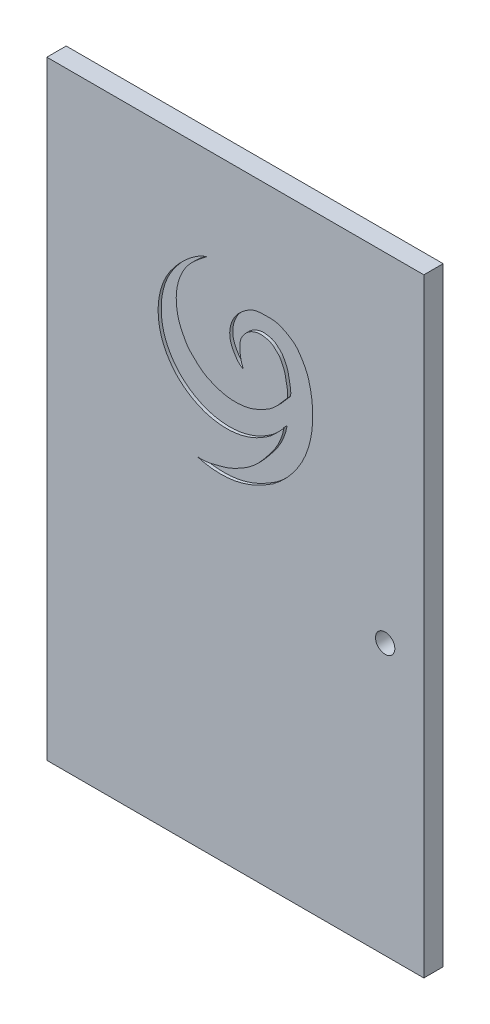
SolidWorks part; units mm, degrees
material "Oak"
ref_plane "Front" through (0, 0, 0) normal (0, 0, 1) x (1, 0, 0)
ref_plane "Top" through (0, 0, 0) normal (0, 1, 0) x (1, 0, 0)
ref_plane "Right" through (0, 0, 0) normal (1, 0, 0) x (0, 0, -1)
sketch "Sketch1" plane through (0, 0, 0) normal (0, 0, 1) x (1, 0, 0)
  line L1 (-61.9125, 200.025) -> (61.9125, 200.025)
  line L2 (-61.9125, 200.025) -> (-61.9125, 0)
  line L3 (-61.9125, 0) -> (61.9125, 0)
  line L4 (61.9125, 200.025) -> (61.9125, 0)
  point P4 (0, 0)
  dimension "D1" = 200.025
  dimension "D2" = 123.825
extrude "Boss-Extrude1" add sketch "Sketch1" along normal blind 6.35
sketch "Sketch2" plane through (0, 0, 6.35) normal (0, 0, 1) x (1, 0, 0)
  line L0 (53.6, 388) -> (369.6, 388) construction
  spline S0 degree 3 poles (-9.3315, 169.5692) (-11.1977, 168.0977) (-14.4737, 165.7212) (-17.3515, 161.5545) (-18.7448, 157.9783) (-19.5701, 154.0018) (-19.3582, 149.9349) (-18.4698, 146.1219) (-17.1242, 143.4447) (-15.644, 140.5996) (-13.5886, 138.6791) (-11.8363, 136.9822) (-10.0773, 135.6789) (-7.8536, 134.5996) (-5.1853, 133.6156) (-2.0478, 132.8976) (1.5194, 132.8413) (5.3924, 133.5155) (8.7623, 135.0635) (13.159, 137.535) (15.4193, 140.6737) (17.1481, 142.5993) knots 0 0 0 0 0.099962 0.167105 0.208449 0.260005 0.33584 0.376754 0.42287 0.460837 0.509981 0.539098 0.563057 0.601179 0.642018 0.681939 0.735202 0.790246 0.844804 0.889641 1 1 1 1
  spline S1 degree 3 poles (17.1481, 142.5993) (17.3676, 144.1387) (16.7335, 146.5811) (16.2785, 149.7656) (15.257, 151.7284) (14.513, 153.197) (13.2408, 154.3756) (11.7456, 155.7813) (9.6838, 156.1936) (7.8174, 156.3969) (6.2038, 155.9782) (4.653, 155.2652) (3.3306, 154.1474) (2.2649, 152.8063) (1.5165, 151.0831) (1.3713, 147.8946) (1.8469, 145.3414) (2.5957, 143.5695) knots 0 0 0 0 0.129227 0.217526 0.27288 0.3187 0.357376 0.421225 0.491052 0.53238 0.581974 0.631698 0.678188 0.729299 0.777919 0.836783 1 1 1 1
  spline S2 degree 3 poles (2.5957, 143.5695) (1.0913, 144.3102) (-0.2193, 146.2154) (-1.5832, 149.0644) (-2.047, 151.8772) (-1.3476, 155.1915) (0.5735, 158.3494) (2.9843, 160.3913) (6.0532, 162.3243) (9.7789, 162.5563) (14.0262, 162.4416) (17.0934, 160.8106) (19.9546, 158.977) (21.7828, 156.3028) (23.6509, 153.0127) (25.2419, 147.2407) (25.7354, 140.3884) (24.6277, 133.6357) (23.0786, 129.0624) (21.1651, 125.2567) (18.8631, 122.0661) (16.7694, 119.5763) (14.7652, 117.6973) (12.4955, 115.7688) (9.6284, 114.0756) (6.5107, 112.4176) (3.2927, 111.1958) (-0.5979, 110.1572) (-5.9978, 109.8213) (-10.1081, 110.3588) (-12.4801, 111.1164) knots 0 0 0 0 0.04258 0.060225 0.083865 0.116965 0.148097 0.180453 0.200375 0.243443 0.276533 0.312238 0.333844 0.366402 0.396661 0.434487 0.524428 0.577121 0.615572 0.652537 0.689999 0.720029 0.738935 0.763057 0.799114 0.827222 0.856964 0.890507 0.934004 1 1 1 1
  spline S3 degree 3 poles (-12.4801, 111.1164) (-10.1295, 110.8518) (-6.7665, 111.677) (-1.9878, 112.9755) (2.1649, 115.0322) (6.5766, 117.9746) (9.9646, 122.0015) (13.7748, 126.7736) (15.5476, 130.8613) (16.0215, 133.6801) knots 0 0 0 0 0.176744 0.265014 0.379274 0.530952 0.667955 0.780622 1 1 1 1
  spline S4 degree 3 poles (16.0215, 133.6801) (15.2848, 132.5464) (13.7295, 131.0702) (11.6647, 129.0106) (9.5977, 127.6645) (7.113, 126.1798) (3.8006, 124.8134) (0.241, 124.0102) (-4.0915, 123.7985) (-9.4114, 124.5192) (-14.8989, 127.0641) (-19.2143, 130.61) (-21.9082, 134.091) (-25.4329, 140.7422) (-25.9034, 149.1421) (-23.0505, 157.0454) (-19.6226, 162.0338) (-15.1359, 166.487) (-11.3442, 168.9289) (-9.3315, 169.5692) knots 0 0 0 0 0.046226 0.074003 0.10038 0.131071 0.17392 0.223492 0.256216 0.323368 0.40673 0.461307 0.514925 0.557489 0.720548 0.782952 0.845979 0.927693 1 1 1 1
  point P26 (-8.8726, 124.7094)
  point P51 (-15.4561, 127.7287)
  point P62 (-7.8969, 134.6688)
  point P70 (-5.1447, 133.6683)
  point P78 (-10.329, 135.9164)
  point P82 (-11.7136, 136.9334)
  point P86 (14.8978, 132.2474)
  point P90 (13.4553, 130.6294)
  point P94 (11.5819, 129.0482)
  point P98 (9.6966, 127.7452)
  point P101 (7.3892, 126.4086)
  point P103 (13.3547, 130.6857)
extrude "Cut-Extrude1" cut sketch "Sketch2" against normal blind 1
sketch "Sketch3" plane through (0, 0, 0) normal (0, 0, 1) x (1, 0, 0)
  line L0 (-61.9125, 0) -> (61.9125, 0) construction
  line L1 (61.9125, 0) -> (61.9125, 200.025) construction
  circle A0 centre (49.2125, 88.9) radius 3.175
  dimension "D1" = 6.35
  dimension "D2" = 88.9
  dimension "D3" = 12.7
extrude "Cut-Extrude5" cut sketch "Sketch3" along normal up to surface (6.35 mm away) up to face at (2.7907, 140.1069, 6.35)
